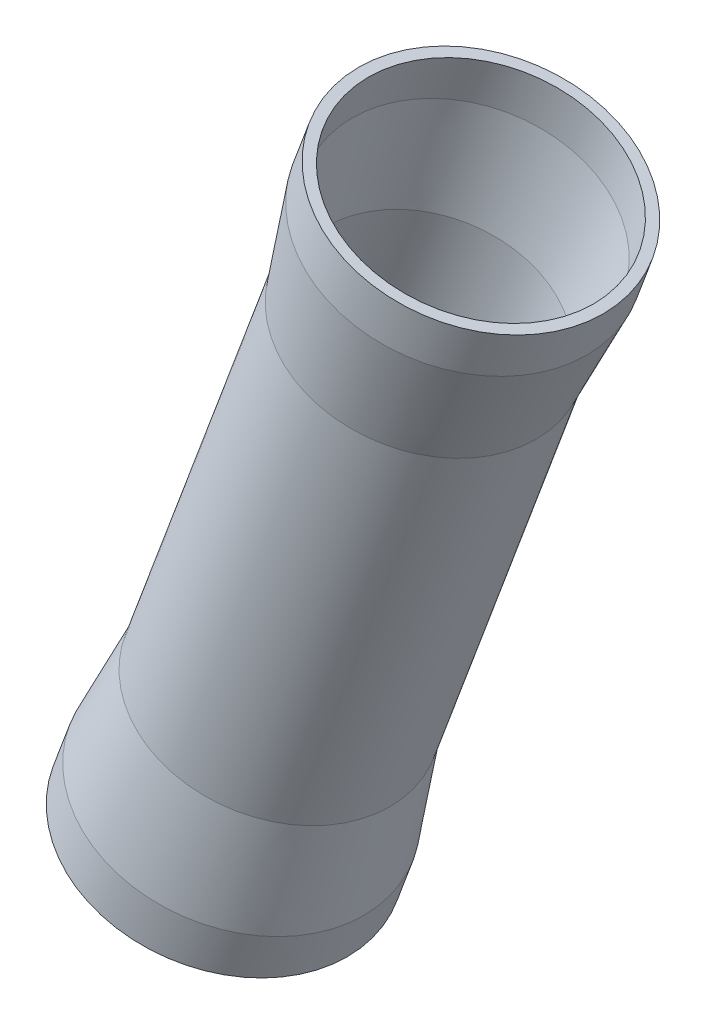
SolidWorks part; units mm, degrees
ref_plane "Plan de face" through (0, 0, 0) normal (0, 0, 1) x (1, 0, 0)
ref_plane "Plan de dessus" through (0, 0, 0) normal (0, 1, 0) x (1, 0, 0)
ref_plane "Plan de droite" through (0, 0, 0) normal (1, 0, 0) x (0, 0, -1)
sketch "Esquisse1" plane through (0, 0, 0) normal (0, 0, 1) x (1, 0, 0)
  line L0 (0, 0) -> (-619.8563, 51.5961) construction
  line L1 (0, 0) -> (-389.1874, 545.3743) construction
  line L2 (0, 0) -> (457.0972, 51.5961) construction
  line L3 (0, 0) -> (163.4516, 525.8703) construction
  line L4 (132.0822, 424.9462) -> (457.0972, 51.5961) construction
  line L5 (-489.2424, 277.5909) -> (-356.2649, 633.487) construction
  line L6 (-379.7372, 570.6665) -> (-22.8665, 389.9919) construction
  line L7 (-22.8665, 389.9919) -> (129.7077, 417.3067) construction
  dimension "D1" = 622
  dimension "D2" = 670
  dimension "D3" = 545
  dimension "D4" = 460
  dimension "D5" = 445
  dimension "D6" = 495
  dimension "D7" = 535
  dimension "D8" = 27
  dimension "D9" = 8
  dimension "D10" = 155
  dimension "D11" = 400
  dimension "D12" = 56
sketch "Esquisse2" plane through (0, 0, 0) normal (0, 0, 1) x (1, 0, 0)
  line L0 (-437.5991, 415.8072) -> (-325.41, 716.066) construction
  line L1 (-489.2424, 277.5909) -> (-356.2649, 633.487) construction
  line L2 (-393.7057, 604.7088) -> (-370.287, 595.9586)
  line L3 (-393.7057, 604.7088) -> (-396.8558, 596.2781)
  line L4 (-489.9188, 565.9313) -> (-384.8241, 526.6636) construction
  line L5 (-396.8558, 596.2781) -> (-401.8641, 575.7314)
  line L6 (-442.7068, 473.5643) -> (-439.5567, 481.995)
  line L7 (-439.5567, 481.995) -> (-429.8647, 500.7916)
  line L8 (-442.7068, 473.5643) -> (-419.2881, 464.8141)
  line L9 (-419.2881, 464.8141) -> (-370.287, 595.9586)
  line L10 (-429.8647, 500.7916) -> (-401.8641, 575.7314)
  point P14 (0, 0)
  dimension "D1" = 50
  dimension "D2" = 140
  dimension "D3" = 45
  dimension "D4" = 9
  dimension "D5" = 80
  dimension "D6" = 27
revolve "Révolution1" add sketch "Esquisse2" angle 360 about L0
shell "Coque1" thickness 2
